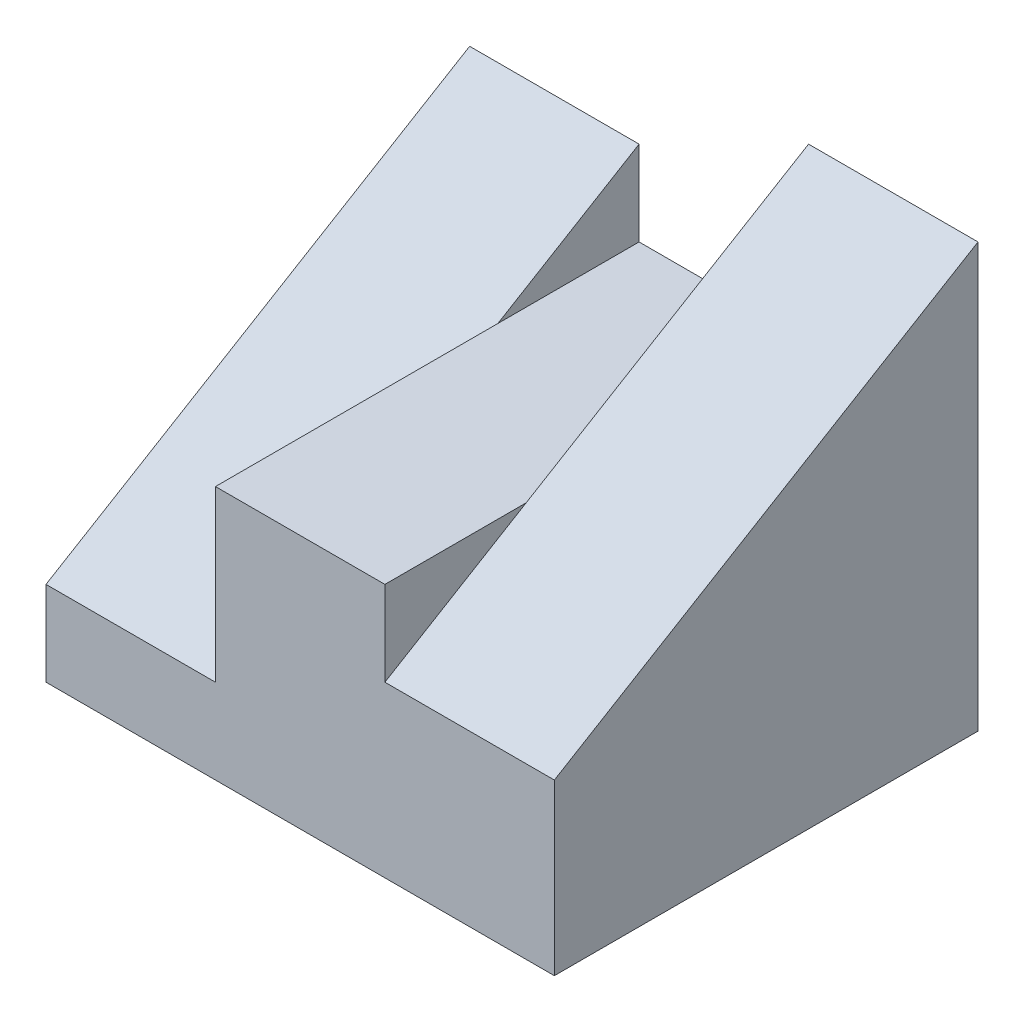
SolidWorks part; units mm, degrees
ref_plane "Front Plane" through (0, 0, 0) normal (0, 0, 1) x (1, 0, 0)
ref_plane "Top Plane" through (0, 0, 0) normal (0, 1, 0) x (1, 0, 0)
ref_plane "Right Plane" through (0, 0, 0) normal (1, 0, 0) x (0, 0, -1)
sketch "Sketch1" plane through (0, 0, 0) normal (0, 0, 1) x (1, 0, 0)
  line L0 (-30, 5) -> (-20, 5)
  line L1 (-20, 5) -> (-20, 15)
  line L2 (-20, 15) -> (-10, 15)
  line L3 (-10, 15) -> (-10, 10)
  line L4 (-10, 10) -> (0, 10)
  line L5 (0, 10) -> (0, 0)
  line L6 (0, 0) -> (-30, 0)
  line L7 (-30, 0) -> (-30, 5)
  dimension "D1" = 5
  dimension "D2" = 30
  dimension "D3" = 10
  dimension "D4" = 10
  dimension "D5" = 5
  dimension "D6" = 10
extrude "Boss-Extrude1" add sketch "Sketch1" along normal blind 25
sketch "Sketch2" plane through (-10, 0, 0) normal (1, 0, 0) x (0, 0, -1)
  line L0 (-25, 10) -> (0, 10)
  line L1 (0, 10) -> (0, 25)
  line L2 (0, 25) -> (-25, 10)
  dimension "D1" = 15
extrude "Boss-Extrude2" add sketch "Sketch2" along normal blind 10
sketch "Sketch3" plane through (-20, 0, 0) normal (-1, 0, 0) x (0, 0, 1)
  line L0 (0, 5) -> (0, 20)
  line L1 (0, 15) -> (0, 5) construction
  line L2 (0, 20) -> (25, 5)
  line L3 (25, 5) -> (0, 5)
  dimension "D1" = 15
extrude "Boss-Extrude3" add sketch "Sketch3" along normal blind 10
